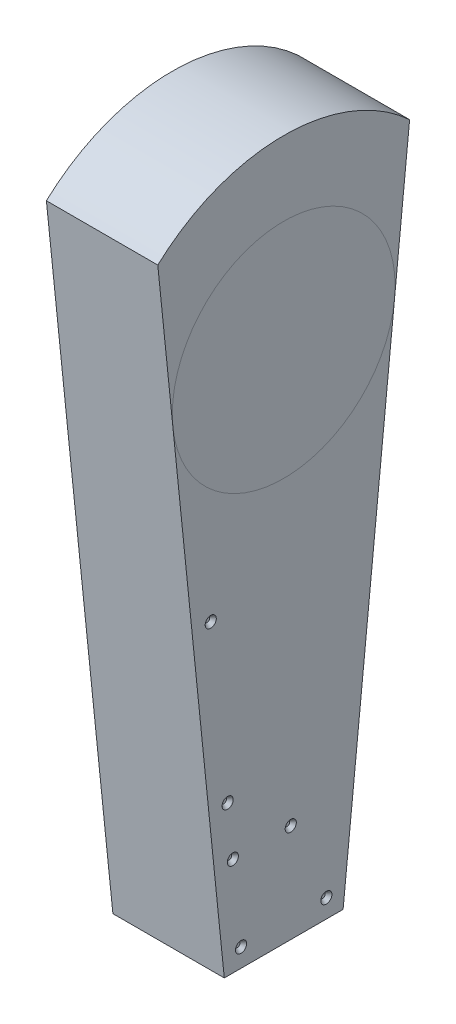
SolidWorks part; units mm, degrees
ref_plane "Alzado" through (0, 0, 0) normal (0, 0, 1) x (1, 0, 0)
ref_plane "Planta" through (0, 0, 0) normal (0, 1, 0) x (1, 0, 0)
ref_plane "Vista lateral" through (0, 0, 0) normal (1, 0, 0) x (0, 0, -1)
sketch "Croquis1" plane through (0, 0, 0) normal (1, 0, 0) x (0, 0, -1)
  line L0 (-40.64, -351.79) -> (-86.1359, 93.3253)
  line L1 (0, 0) -> (0, -351.79) construction
  line L2 (40.64, -351.79) -> (86.1359, 93.3253)
  line L7 (-40.64, -351.79) -> (40.64, -351.79)
  circle A0 centre (0, 0) radius 127 construction
  circle A1 centre (0, 0) radius 76.2 construction
  arc A4 (86.1359, 93.3253) -> (-86.1359, 93.3253) centre (0, 0) ccw
  dimension "D1" = 254
  dimension "D2" = 152.4
  dimension "D3" = 351.79
extrude "Saliente-Extruir1" add sketch "Croquis1" along normal blind 76.2
sketch "Croquis2" plane through (76.2, 0, 0) normal (1, 0, 0) x (0, 0, -1)
  circle A0 centre (0, 0) radius 76.2
split line "Línea de partición1"
sketch "Croquis3" plane through (0, -351.79, 0) normal (0, -1, 0) x (1, 0, 0)
  line L0 (0, 0) -> (38.1, 0) construction
  line L1 (38.1, 0) -> (38.1, 40.64) construction
  line L2 (76.2, 40.64) -> (0, 40.64) construction
  circle A0 centre (38.1, 0) radius 25.4
  dimension "D1" = 50.8
split line "Línea de partición2"
sketch "Croquis4" plane through (76.2, 0, 0) normal (1, 0, 0) x (0, 0, -1)
  line L6 (-53.5213, -100.8643) -> (-29.1719, -339.09) construction
  line L7 (-29.1719, -339.09) -> (29.1719, -339.09) construction
  line L8 (29.1719, -339.09) -> (53.2304, -103.711) construction
  circle A0 centre (-49.9171, -136.1268) radius 3.81
  circle A1 centre (-38.3624, -249.174) radius 3.81
  circle A2 centre (-34.7681, -284.3391) radius 3.81
  circle A3 centre (-29.1719, -339.09) radius 3.81
  circle A4 centre (29.1719, -339.09) radius 3.81
  circle A5 centre (4.8195, -284.3391) radius 3.81
  dimension "D1" = 7.62
extrude "Cortar-Extruir1" cut sketch "Croquis4" against normal blind 2.54 draft 39
sketch "Croquis5" plane through (0, 0, 0) normal (-1, 0, 0) x (0, 0, 1)
  line L3 (0, -339.09) -> (0, -280.0103) construction
  line L6 (-29.1719, -339.09) -> (-72.8345, 88.0887) construction
  line L7 (72.8345, 88.0887) -> (29.1719, -339.09) construction
  line L8 (29.1719, -339.09) -> (-29.1719, -339.09) construction
  circle A1 centre (-12.5569, -339.09) radius 3.81
  arc A2 (72.8345, 88.0887) -> (-72.8345, 88.0887) centre (0, 0) ccw construction
  circle A3 centre (12.5569, -339.09) radius 3.81
  circle A4 centre (-34.1821, -290.0722) radius 3.81
  circle A5 centre (-48.2655, -152.2857) radius 3.81
  circle A6 centre (-69.7519, 57.9299) radius 3.81
  circle A7 centre (-48.2655, 103.6095) radius 3.81
  circle A8 centre (48.2655, 103.6095) radius 3.81
  circle A9 centre (69.7519, 57.9299) radius 3.81
  circle A10 centre (48.2655, -152.2857) radius 3.81
  dimension "D1" = 7.62
extrude "Cortar-Extruir2" cut sketch "Croquis5" against normal blind 2.54 draft 39
